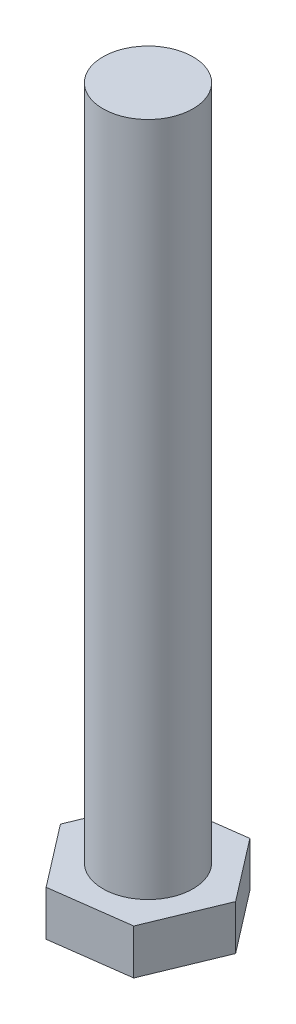
SolidWorks part; units mm, degrees
ref_plane "Front Plane" through (0, 0, 0) normal (0, 0, 1) x (1, 0, 0)
ref_plane "Top Plane" through (0, 0, 0) normal (0, 1, 0) x (1, 0, 0)
ref_plane "Right Plane" through (0, 0, 0) normal (1, 0, 0) x (0, 0, -1)
sketch "Sketch1" plane through (0, 0, 0) normal (0, 1, 0) x (1, 0, 0)
  line L1 (2.1121, -2.7457) -> (3.4339, 0.4563)
  line L2 (3.4339, 0.4563) -> (1.3218, 3.202)
  line L3 (1.3218, 3.202) -> (-2.1121, 2.7457)
  line L4 (-2.1121, 2.7457) -> (-3.4339, -0.4563)
  line L5 (-3.4339, -0.4563) -> (-1.3218, -3.202)
  line L6 (-1.3218, -3.202) -> (2.1121, -2.7457)
  circle A0 centre (0, 0) radius 3 construction
  dimension "D1" = 6
extrude "Boss-Extrude1" add sketch "Sketch1" along normal blind 2
sketch "Sketch2" plane through (0, 2, 0) normal (0, 1, 0) x (1, 0, 0)
  circle A0 centre (0, 0) radius 2
  dimension "D1" = 4
extrude "Boss-Extrude2" add sketch "Sketch2" along normal blind 30
